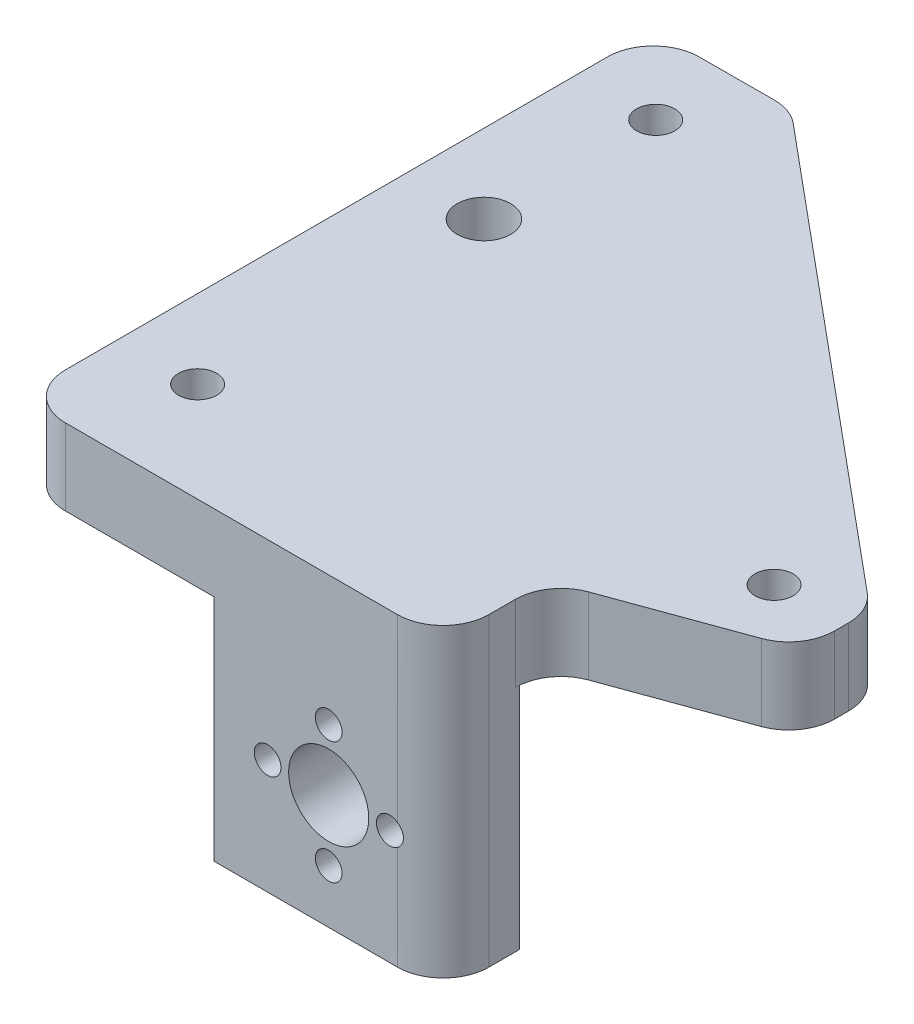
SolidWorks part; units mm, degrees
ref_plane "Front Plane" through (0, 0, 0) normal (0, 0, 1) x (1, 0, 0)
ref_plane "Top Plane" through (0, 0, 0) normal (0, 1, 0) x (1, 0, 0)
ref_plane "Right Plane" through (0, 0, 0) normal (1, 0, 0) x (0, 0, -1)
sketch "Sketch1" plane through (0, 0, 0) normal (0, 1, 0) x (1, 0, 0)
  line L0 (0, 6) -> (0, 77.0213)
  line L3 (10.3, 73.0366) -> (10.3, 28.0366) construction
  line L6 (5.9787, 83.0213) -> (15.8161, 83.0562)
  line L7 (19.6778, 81.6662) -> (77.8404, 33.2134)
  line L8 (80, 28.6035) -> (80, 26.7674)
  line L9 (6, 0) -> (25.5, 0)
  line L10 (59.4479, 15.0858) -> (76.0521, 21.1293)
  line L11 (25.5, 0) -> (49.5, 0)
  line L12 (55.5, 6) -> (55.5, 9.4477)
  circle A0 centre (10.3, 73.0366) radius 2.5
  circle A1 centre (10.3, 13.0366) radius 2.5
  circle A2 centre (70.8, 28.0366) radius 2.5
  circle A3 centre (10.3, 50.5366) radius 3.5
  arc A4 (80, 26.7674) -> (76.0521, 21.1293) centre (74, 26.7674) cw
  arc A6 (0, 6) -> (6, 0) centre (6, 6) ccw
  arc A7 (77.8404, 33.2134) -> (80, 28.6035) centre (74, 28.6035) cw
  arc A8 (15.8161, 83.0562) -> (19.6778, 81.6662) centre (15.8374, 77.0563) cw
  arc A9 (0, 77.0213) -> (5.9787, 83.0213) centre (6, 77.0213) cw
  arc A10 (49.5, 0) -> (55.5, 6) centre (49.5, 6) ccw
  arc A11 (55.5, 9.4477) -> (59.4479, 15.0858) centre (61.5, 9.4477) cw
  point P4 (166.575, 29.3717)
  point P22 (80, 22.5662)
  point P25 (17.9999, 0)
  point P28 (0, 0)
  point P31 (80, 31.4143)
  point P34 (17.9999, 83.064)
  point P37 (0, 83)
  point P42 (55.5, 0)
  dimension "D4" = 5
  dimension "D5" = 5
  dimension "D6" = 5
  dimension "D7" = 7
  dimension "D9" = 83
  dimension "D17" = 6
  dimension "D19" = 6
  dimension "D20" = 6
  dimension "D1" = 60
  dimension "D2" = 45
  dimension "D3" = 60.5
  dimension "D8" = 10.3
  dimension "D10" = 10
  dimension "D11" = 18
  dimension "D12" = 22.5
  dimension "D13" = 20
  dimension "D14" = 40
  dimension "D15" = 8.8481
  dimension "D16" = 80
  dimension "D18" = 45.2
  dimension "D21" = 24
extrude "Boss-Extrude2" add sketch "Sketch1" along normal blind 10 contours L0 A9 L6 A8 L7 A7 L8 A4 L10 L12 L11 L9 A6
sketch "Sketch5" plane through (0, 0, 0) normal (0, 1, 0) x (1, 0, 0)
  line L1 (55.5, 6) -> (55.5, 10)
  line L2 (55.5, 6) -> (55.5, 9.4477) construction
  line L3 (55.5, 10) -> (25.5, 10)
  line L4 (25.5, 10) -> (25.5, 0)
  line L5 (6, 0) -> (49.5, 0) construction
  line L7 (25.5, 0) -> (49.5, 0)
  arc A0 (49.5, 0) -> (55.5, 6) centre (49.5, 6) ccw
  dimension "D1" = 6
  dimension "D2" = 10
  dimension "D3" = 30
  dimension "D4" = 4
extrude "Boss-Extrude4" add sketch "Sketch5" against normal blind 30 from surface at 0 starting at face at (70.8, 0, -25.5366)
sketch "Sketch6" plane through (0, 0, -10) normal (0, 0, -1) x (-1, 0, 0)
  line L0 (-55.5, -30) -> (-55.5, 0) construction
  line L1 (-55.5, -30) -> (-25.5, -30) construction
  line L2 (-48.7776, -15) -> (-31.1819, -15) construction
  line L3 (-40.5, -8.2453) -> (-40.5, -21.5651) construction
  circle A0 centre (-40.5, -15) radius 11
  circle A1 centre (-40.5, -15) radius 8
  circle A2 centre (-40.5, -7) radius 1.75
  circle A3 centre (-40.5, -23) radius 1.75
  circle A4 centre (-48.5, -15) radius 1.75
  circle A5 centre (-32.5, -15) radius 1.75
  circle A6 centre (-40.5, -15) radius 5.25
  dimension "D1" = 22
  dimension "D4" = 3.5
  dimension "D5" = 16
  dimension "D6" = 3.5
  dimension "D7" = 10.5
  dimension "D2" = 15
  dimension "D3" = 15
extrude "Cut-Extrude1" cut sketch "Sketch6" against normal through all contours A5 | A3 | A4 | A2 | A6
